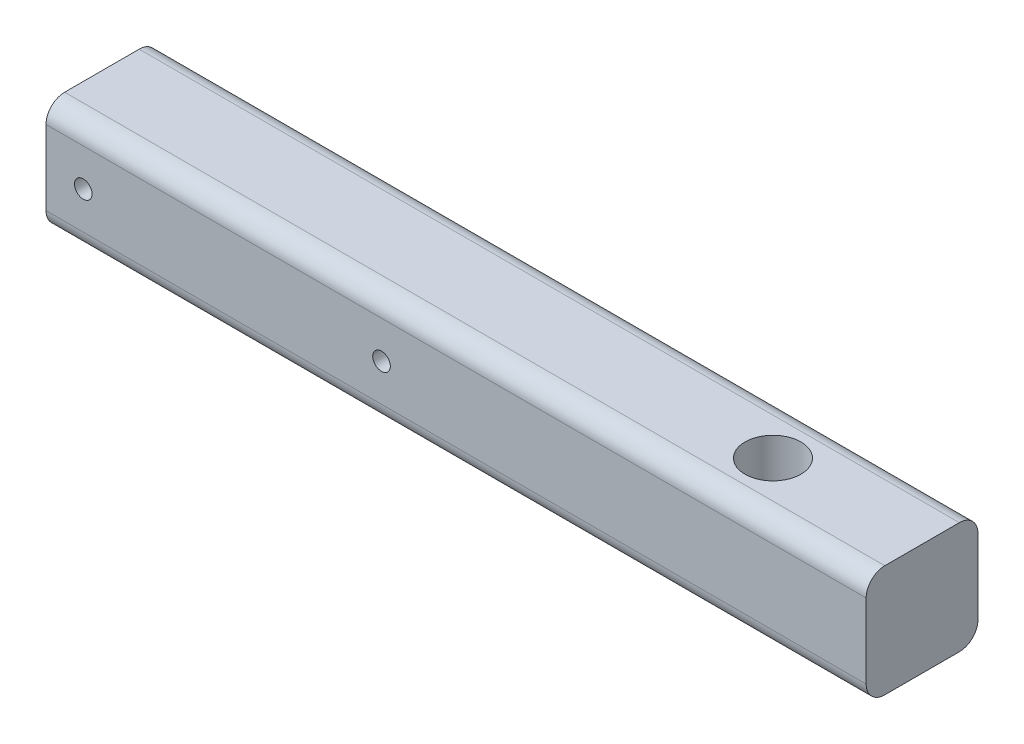
SolidWorks part; units mm, degrees
ref_plane "Front Plane" through (0, 0, 0) normal (0, 0, 1) x (1, 0, 0)
ref_plane "Top Plane" through (0, 0, 0) normal (0, 1, 0) x (1, 0, 0)
ref_plane "Right Plane" through (0, 0, 0) normal (1, 0, 0) x (0, 0, -1)
sketch "Sketch1" plane through (0, 0, 0) normal (1, 0, 0) x (0, 0, -1)
  line L1 (-9.525, -9.525) -> (9.525, -9.525)
  line L2 (-9.525, -9.525) -> (-9.525, 9.525)
  line L3 (-9.525, 9.525) -> (9.525, 9.525)
  line L4 (9.525, -9.525) -> (9.525, 9.525)
  line L5 (-9.525, -9.525) -> (9.525, 9.525) construction
  line L6 (-9.525, 9.525) -> (9.525, -9.525) construction
  point P0 (0, 0)
  dimension "D1" = 19.05
extrude "Boss-Extrude1" add sketch "Sketch1" along normal blind 139.7 contours L2 L3 L4 L1
sketch "Sketch2" plane through (0, 9.525, 0) normal (0, 1, 0) x (1, 0, 0)
  line L0 (139.7, -9.525) -> (139.7, 9.525) construction
  circle A0 centre (114.3, 0) radius 4.7625
  dimension "D1" = 9.525
  dimension "D2" = 25.4
extrude "Cut-Extrude1" cut sketch "Sketch2" against normal through all
sketch "Sketch3" plane through (0, 0, 9.525) normal (0, 0, 1) x (1, 0, 0)
  line L1 (0, -9.525) -> (0, 9.525) construction
  circle A0 centre (6.35, 0) radius 1.5
  circle A1 centre (57.15, 0) radius 1.5
  point P7 (0, 0)
  dimension "D1" = 3
  dimension "D2" = 50.8
  dimension "D3" = 6.35
extrude "Cut-Extrude2" cut sketch "Sketch3" against normal through all
fillet "Fillet1" radius 3.175 4 edges at (69.85, -9.525, -9.525) (69.85, -9.525, 9.525) (69.85, 9.525, -9.525) (69.85, 9.525, 9.525)
